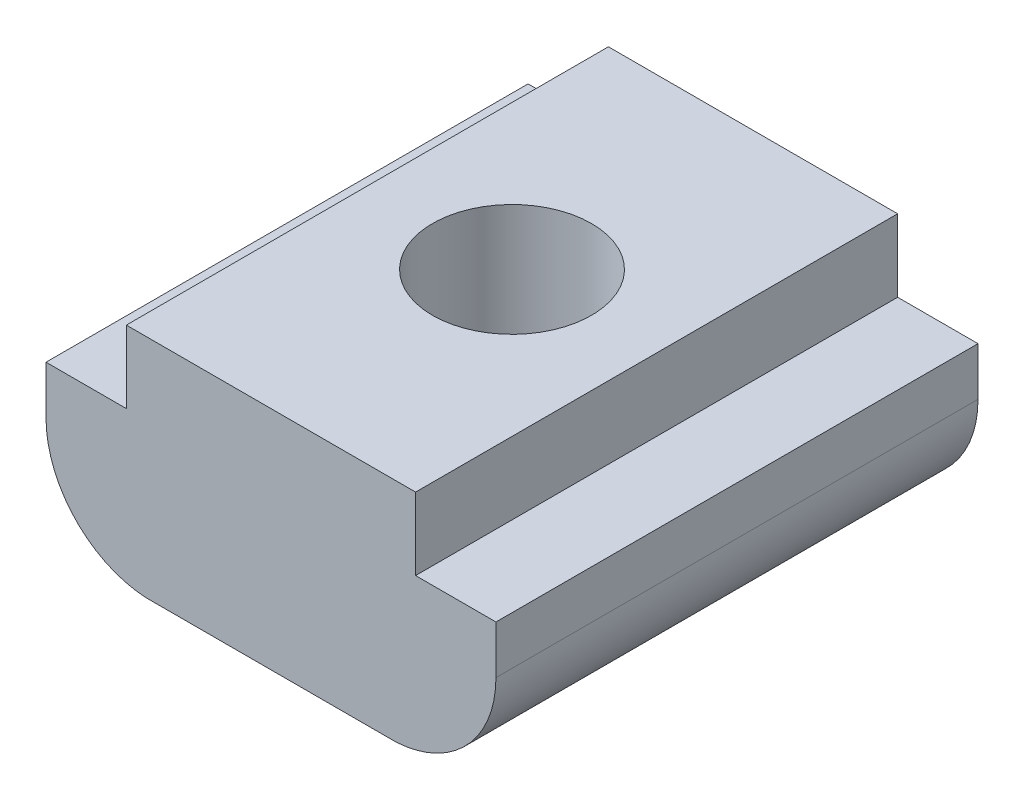
SolidWorks part; units mm, degrees
ref_plane "前视基准面" through (0, 0, 0) normal (0, 0, 1) x (1, 0, 0)
ref_plane "上视基准面" through (0, 0, 0) normal (0, 1, 0) x (1, 0, 0)
ref_plane "右视基准面" through (0, 0, 0) normal (1, 0, 0) x (0, 0, -1)
sketch "草图1" plane through (0, 0, 0) normal (0, 0, 1) x (1, 0, 0)
  line L0 (3, 3) -> (-3, 3)
  line L1 (0, 3) -> (0, -1.6938) construction
  line L2 (-3, 3) -> (-3, 1.5)
  line L3 (4.6667, 1.5) -> (-4.6667, 1.5) construction
  line L4 (-3, 1.5) -> (-4.6667, 1.5)
  line L5 (2.6, -1.6938) -> (-2.6, -1.6938)
  line L6 (-4.6667, 1.5) -> (-4.6667, 0.5)
  line L7 (3, 3) -> (3, 1.5)
  line L8 (3, 1.5) -> (4.6667, 1.5)
  line L9 (4.6667, 1.5) -> (4.6667, 0.5)
  arc A0 (-4.6667, 0.5) -> (-2.6, -1.6938) centre (-2.4691, 0.5) ccw
  arc A1 (4.6667, 0.5) -> (2.6, -1.6938) centre (2.4691, 0.5) cw
  point P8 (0, 1.5)
  point P17 (0, -1.6938)
extrude "凸台-拉伸1" add sketch "草图1" along normal blind 10
hole_wizard "M4 螺纹孔1" positions "草图12" profile "草图13" tap size "M4" standard "ISO" end condition through all
sketch "草图12" plane through (0, 3, 0) normal (0, 1, 0) x (1, 0, 0)
  point P0 (0, -5)
sketch "草图13" plane through (0, 3, 5) normal (1, 0, 0) x (0, 0, 1)
  line L0 (0, 0) -> (0, 4.6938)
  line L1 (0, 4.6938) -> (1.65, 4.6938)
  line L2 (1.65, 4.6938) -> (1.65, 0)
  line L5 (1.65, 0) -> (0, 0)
  line L11 (0, -6.35) -> (0, 107.95) construction
  dimension "通孔螺纹孔钻头直径" = 3.3
  dimension "通孔螺纹孔钻头深度" = 4.6938
cosmetic thread "孔螺蚊线4"
move or copy body "实体-移动/复制1" bodies to move or copy 107 copy no translate (0, 0, -5)
